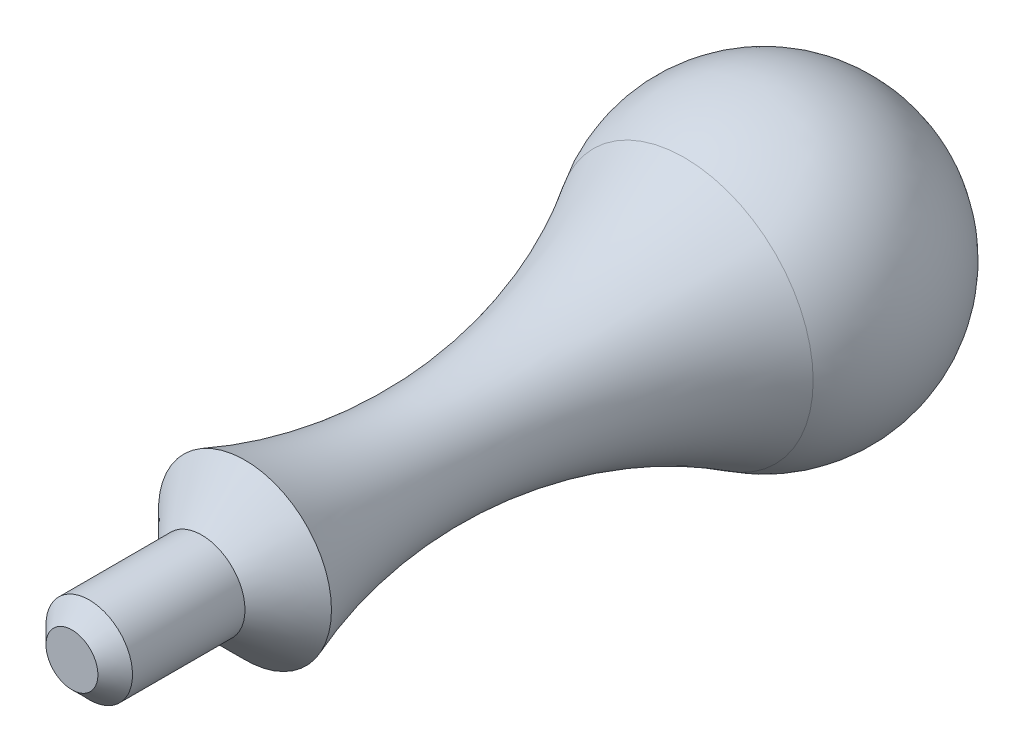
SolidWorks part; units mm, degrees
material "AISI 1020 Steel, Cold Rolled"
ref_plane "Front" through (0, 0, 0) normal (0, 0, 1) x (1, 0, 0)
ref_plane "Top" through (0, 0, 0) normal (0, 1, 0) x (1, 0, 0)
ref_plane "Right" through (0, 0, 0) normal (1, 0, 0) x (0, 0, -1)
sketch "Sketch1" plane through (0, 0, 0) normal (1, 0, 0) x (0, 0, -1)
  line L0 (-56.7528, 0) -> (23.1726, 0) construction
  line L1 (-50.8, 3.175) -> (-41.275, 3.175)
  line L2 (-38.1, 6.35) -> (-41.275, 3.175)
  line L3 (-50.8, 6.9298) -> (-50.8, 0) construction
  line L4 (-12.355, 3.9751) -> (9.2631, 3.9751) construction
  line L5 (-50.8, 3.175) -> (-50.8, 0)
  line L6 (-50.8, -3.0947) -> (-50.8, -11.3869) construction
  line L7 (-50.8, 0) -> (11.1125, 0)
  arc A0 (-38.1, 6.35) -> (-5.8432, 9.4522) centre (-25.1197, 40.6351) ccw
  arc A1 (11.1125, 0) -> (-5.8432, 9.4522) centre (0, 0) ccw
  dimension "D4" = 22.225
  dimension "D1" = 45
  dimension "D2" = 12.7
  dimension "D3" = 9.525
  dimension "D5" = 50.8
  dimension "D6" = 3.9751
  dimension "D7" = 6.35
revolve "Revolve1" add sketch "Sketch1" angle 360 about L0
cosmetic thread "Cosmetic Thread1" parameters "D2"=4.8387
chamfer "Chamfer1" distance 1.27 angle 45 1 edges at (3.175, 0, 50.8)
